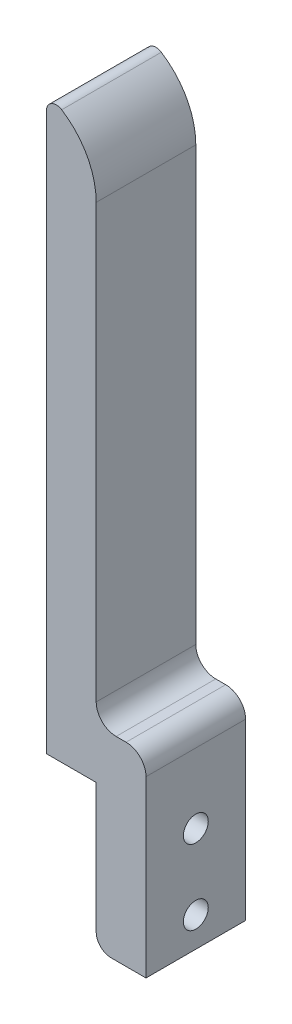
SolidWorks part; units mm, degrees
ref_plane "Front Plane" through (0, 0, 0) normal (0, 0, 1) x (1, 0, 0)
ref_plane "Top Plane" through (0, 0, 0) normal (0, 1, 0) x (1, 0, 0)
ref_plane "Right Plane" through (0, 0, 0) normal (1, 0, 0) x (0, 0, -1)
sketch "Sketch1" plane through (0, 0, 0) normal (0, 0, 1) x (1, 0, 0)
  line L0 (0, 0) -> (10, 0)
  line L1 (10, 0) -> (10, -29)
  line L2 (10, -29) -> (20, -29)
  line L3 (20, -29) -> (20, 6)
  line L4 (16, 10) -> (14, 10)
  line L5 (10, 14) -> (10, 100.8579)
  line L6 (0, 0) -> (0, 111.8123)
  arc A0 (10, 100.8579) -> (3.0769, 113.4976) centre (-5, 100.8579) ccw
  arc A1 (0, 111.8123) -> (3.0769, 113.4976) centre (2, 111.8123) cw
  arc A2 (20, 6) -> (16, 10) centre (16, 6) ccw
  arc A3 (14, 10) -> (10, 14) centre (14, 14) cw
  point P12 (0, 115)
  dimension "D2" = 15
  dimension "D8" = 2
  dimension "D9" = 4
  dimension "D1" = 10
  dimension "D3" = 115
  dimension "D4" = 29
  dimension "D5" = 10
  dimension "D6" = 10
  dimension "D7" = 10
extrude "Boss-Extrude1" add sketch "Sketch1" along normal blind 20
sketch "Sketch2" plane through (20, 0, 0) normal (1, 0, 0) x (0, 0, -1)
  line L0 (-10, -29) -> (-10, 29.9824) construction
  line L1 (-20, -29) -> (0, -29) construction
  circle A0 centre (-10, -8) radius 2.5
  circle A1 centre (-10, -23) radius 2.5
  dimension "D1" = 5
extrude "Cut-Extrude1" cut sketch "Sketch2" against normal through all
fillet "Fillet1" radius 3 1 edges at (10, -29, 10)
